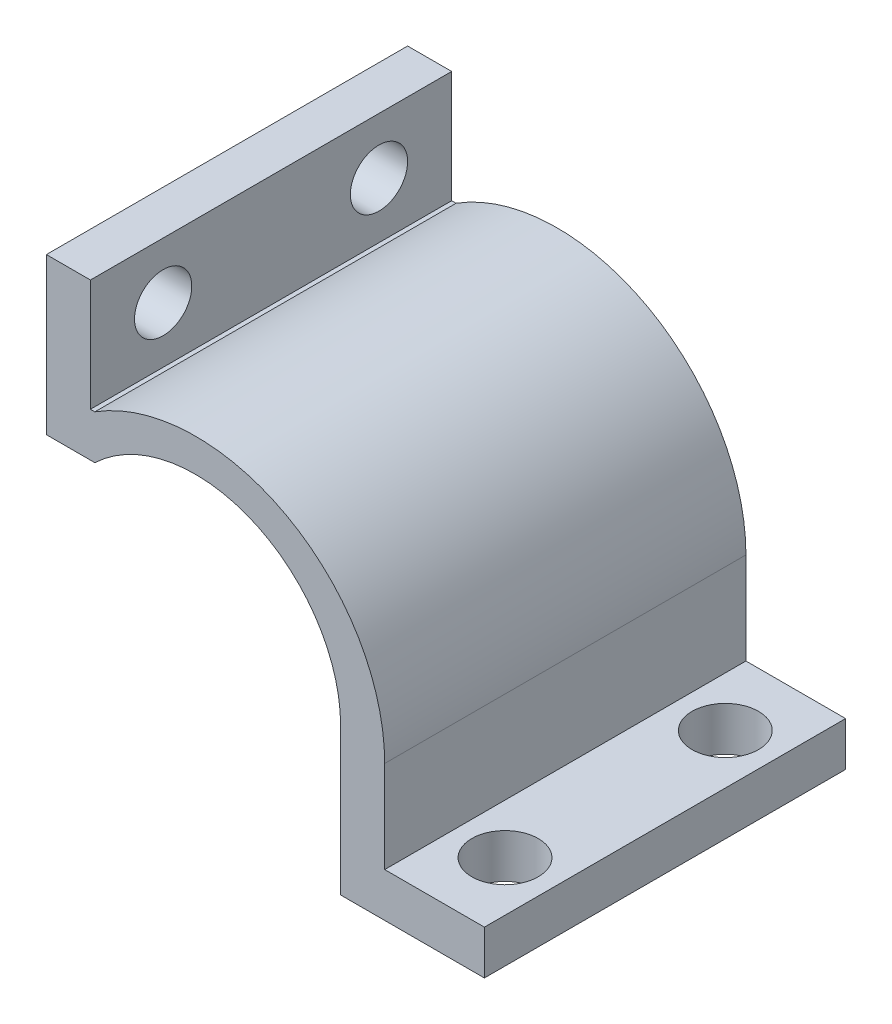
SolidWorks part; units mm, degrees
ref_plane "Front Plane" through (0, 0, 0) normal (0, 0, 1) x (1, 0, 0)
ref_plane "Top Plane" through (0, 0, 0) normal (0, 1, 0) x (1, 0, 0)
ref_plane "Right Plane" through (0, 0, 0) normal (1, 0, 0) x (0, 0, -1)
sketch "Sketch1" plane through (0, 0, 0) normal (0, 0, 1) x (1, 0, 0)
  line L0 (0, 0) -> (33.0033, 0) construction
  line L1 (33.0033, 0) -> (33.0033, -33.228)
  line L2 (33.0033, -33.228) -> (0, -33.228) construction
  line L3 (33.0033, -33.228) -> (65.6321, -33.228)
  line L4 (65.6321, -33.228) -> (65.6321, -23.228)
  line L5 (65.6321, -23.228) -> (43.0033, -23.228)
  line L6 (43.0033, -23.228) -> (43.0033, -2.3696)
  line L7 (0, 0) -> (-33.7938, 0) construction
  line L8 (-33.7938, 0) -> (-33.7938, 50.6526) construction
  line L9 (-22.7938, 23.8598) -> (-33.7938, 23.8598)
  line L10 (-33.7938, 23.8598) -> (-33.7938, 59.2751)
  line L11 (-33.7938, 59.2751) -> (-23.7938, 59.2751)
  line L12 (-23.7938, 59.2751) -> (-23.7938, 33.8598)
  line L13 (-23.7938, 33.8598) -> (-22.7938, 33.8598)
  circle A0 centre (0, 0) radius 33.228 construction
  arc A1 (-22.7938, 23.8598) -> (33.0033, 0) centre (0.0033, 0) cw
  arc A2 (-22.7938, 33.8598) -> (43.0033, -2.3696) centre (0.1304, -2.3696) cw
  dimension "D1" = 10
  dimension "D2" = 10
  dimension "D3" = 10
  dimension "10" = 10
extrude "Boss-Extrude1" add sketch "Sketch1" against normal blind 82
sketch "Sketch3" plane through (0, -23.228, 0) normal (0, 1, 0) x (1, 0, 0)
  line L0 (54.3177, 82) -> (54.3177, 73.5375) construction
  line L1 (54.3177, 8.4625) -> (54.3177, 0) construction
  line L2 (65.6321, 82) -> (43.0033, 82) construction
  line L3 (65.6321, 0) -> (43.0033, 0) construction
  line L4 (43.0033, 66) -> (46.7803, 66) construction
  line L5 (43.0033, 82) -> (43.0033, 0) construction
  line L6 (61.8552, 66) -> (65.6321, 66) construction
  line L7 (65.6321, 82) -> (65.6321, 0) construction
  circle A0 centre (54.3177, 16) radius 7.5375
  circle A1 centre (54.3177, 66) radius 7.5375
extrude "Cut-Extrude2" cut sketch "Sketch3" against normal through all
sketch "Sketch4" plane through (-23.7938, 0, 0) normal (1, 0, 0) x (0, 0, -1)
  line L0 (10, 46.5675) -> (0, 46.5675) construction
  line L1 (0, 33.8598) -> (0, 59.2751) construction
  line L2 (16.5, 53.0675) -> (16.5, 59.2751) construction
  line L3 (82, 59.2751) -> (0, 59.2751) construction
  line L4 (72, 46.5675) -> (82, 46.5675) construction
  line L5 (82, 33.8598) -> (0, 33.8598) construction
  line L6 (16.5, 33.8598) -> (16.5, 40.0675) construction
  line L7 (82, 33.8598) -> (82, 59.2751) construction
  circle A0 centre (16.5, 46.5675) radius 6.5
  circle A1 centre (65.5, 46.5675) radius 6.5
  dimension "D1" = 10
  dimension "D2" = 13
extrude "Cut-Extrude3" cut sketch "Sketch4" against normal through all
